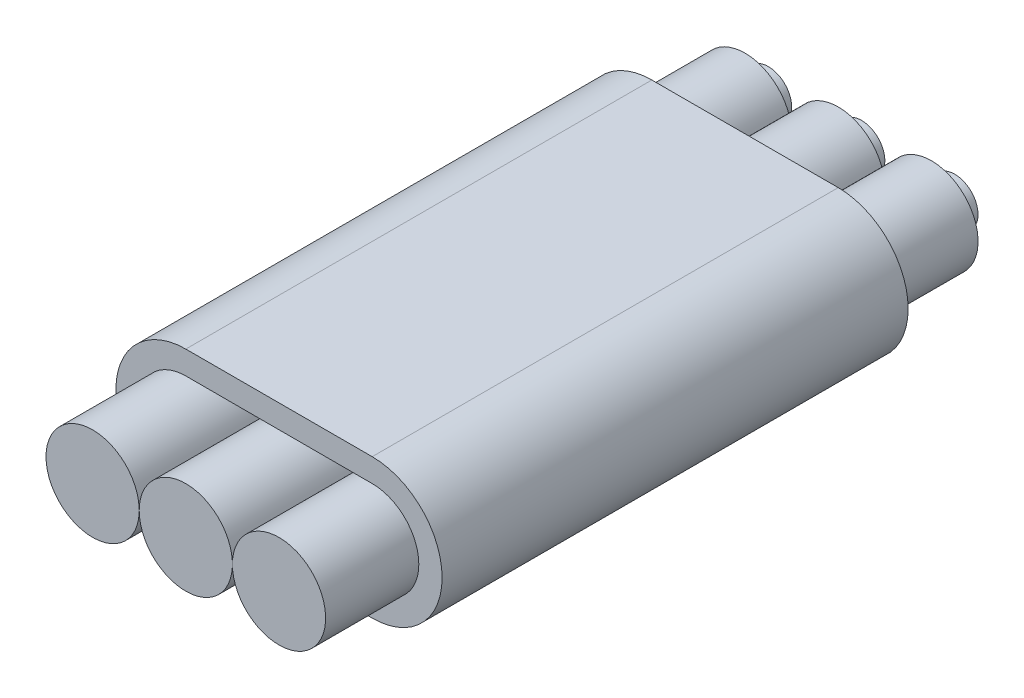
SolidWorks part; units mm, degrees
material "BUTYL"
ref_plane "Front Plane" through (0, 0, 0) normal (0, 0, 1) x (1, 0, 0)
ref_plane "Top Plane" through (0, 0, 0) normal (0, 1, 0) x (1, 0, 0)
ref_plane "Right Plane" through (0, 0, 0) normal (1, 0, 0) x (0, 0, -1)
sketch "Sketch1" plane through (0, 0, 0) normal (0, 0, 1) x (1, 0, 0)
  line L1 (-2, 1) -> (2, 1)
  line L3 (-2, -1) -> (2, -1)
  arc A1 (-2, 1) -> (-2, -1) centre (-2, 0) ccw
  arc A2 (2, -1) -> (2, 1) centre (2, 0) ccw
extrude "Extrude-Thin1" add sketch "Sketch1" along normal blind 10 thin thin type one direction wall 0.5
sketch "Sketch2" plane through (0, 0, 0) normal (0, 0, -1) x (-1, 0, 0)
  circle A0 centre (0, 0) radius 1
  circle A1 centre (2, 0) radius 1
  circle A2 centre (-2, 0) radius 1
extrude "Extrude-Thin2" add sketch "Sketch2" along normal blind 2 and the other way blind 12 thin contours A2 | A0 | A1 thin type one direction reverse wall 0.5
sketch "Sketch3" plane through (0, 0, -2) normal (0, 0, -1) x (-1, 0, 0)
  circle A0 centre (-2, 0) radius 0.5
  circle A1 centre (0, 0) radius 0.5
  circle A2 centre (2, 0) radius 0.5
  circle A3 centre (-2, 0) radius 0.5 construction
  circle A4 centre (0, 0) radius 0.5 construction
  circle A5 centre (2, 0) radius 0.5 construction
extrude "Boss-Extrude1" add sketch "Sketch3" along normal blind 0.5 and the other way up to surface (14 mm away) other way up to face at (-0.5, 0, 12)
